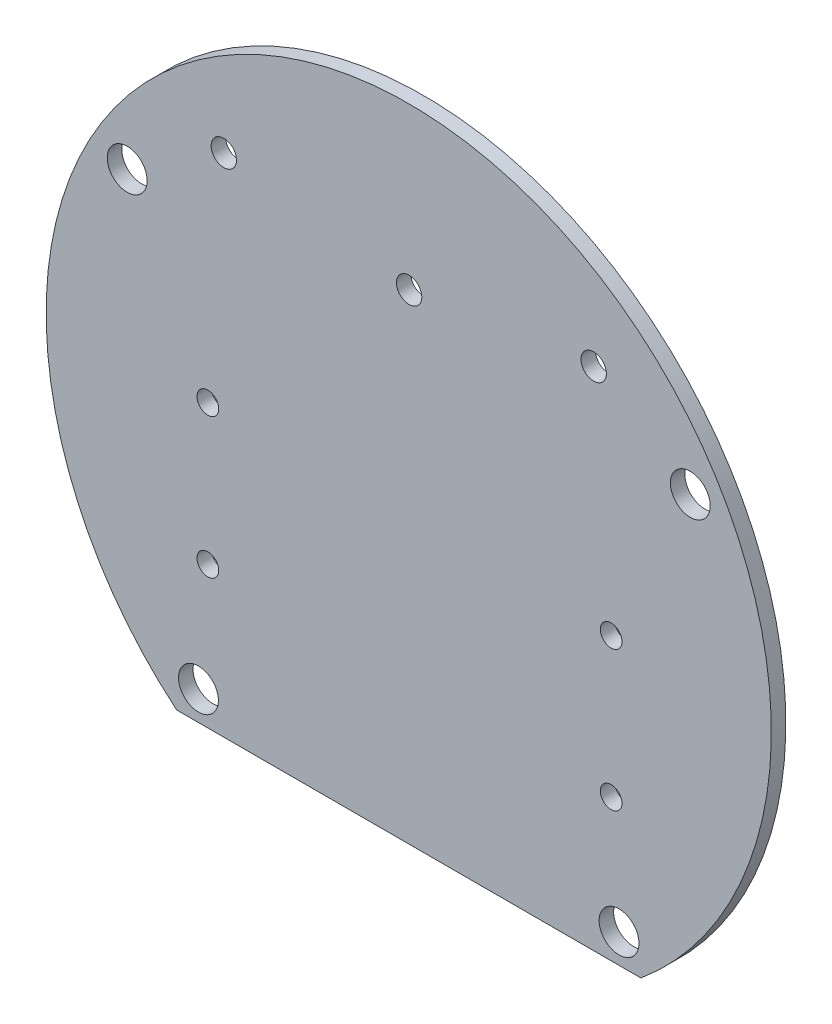
SolidWorks part; units mm, degrees
ref_plane "Plano frontal" through (0, 0, 0) normal (0, 0, 1) x (1, 0, 0)
ref_plane "Plano superior" through (0, 0, 0) normal (0, 1, 0) x (1, 0, 0)
ref_plane "Plano direito" through (0, 0, 0) normal (1, 0, 0) x (0, 0, -1)
sketch "Esboço1" plane through (0, 0, 0) normal (0, 0, 1) x (1, 0, 0)
  circle A0 centre (0, 0) radius 50
  dimension "D1" = 100
extrude "Ressalto-extrusão1" add sketch "Esboço1" along normal blind 2
sketch "Esboço2" plane through (0, 0, 2) normal (0, 0, 1) x (1, 0, 0)
  line L0 (0, 0) -> (0, 68.6386) construction
  line L1 (-61.9657, 0) -> (66.0984, 0) construction
  line L2 (-61.9657, -34.4093) -> (66.0984, -34.4093) construction
  circle A4 centre (-29, -34.4093) radius 2.75
  circle A5 centre (29, -34.4093) radius 2.75
  circle A6 centre (-38.8242, 22.7526) radius 2.75
  circle A7 centre (38.8242, 22.7526) radius 2.75
  point P9 (2.9328, -3.8481)
  dimension "D1" = 58
  dimension "D4" = 45
  dimension "D2" = 45
  dimension "D8" = 5.5
  dimension "D9" = 5.5
  dimension "D10" = 5.5
  dimension "D11" = 5.5
  dimension "D3" = 45
  dimension "D5" = 45
  dimension "D6" = 58
  dimension "D7" = 58
extrude "Corte-extrusão1" cut sketch "Esboço2" against normal blind 2
sketch "Esboço4" plane through (0, 0, 2) normal (0, 0, 1) x (1, 0, 0)
  line L0 (-40.7239, -38.4093) -> (44.5707, -38.4093)
  line L1 (-40.7239, -38.4093) -> (1.9234, -68.0022)
  line L2 (1.9234, -68.0022) -> (44.5707, -38.4093)
  circle A0 centre (-29, -34.4093) radius 2.75 construction
  dimension "D1" = 4
extrude "Corte-extrusão2" cut sketch "Esboço4" against normal blind 10 and the other way through all
sketch "Esboço5" plane through (0, 0, 0) normal (0, 0, -1) x (-1, 0, 0)
  line L0 (65.401, 0) -> (-65.401, 0) construction
  line L2 (0, 53.6175) -> (0, -45.5551) construction
  circle A1 centre (-27.91, -18.86) radius 1.5
  circle A2 centre (27.7, -18.86) radius 1.5
  circle A3 centre (27.7, 0.44) radius 1.5
  circle A4 centre (-27.91, 0.44) radius 1.5
  circle A5 centre (25.5, 31.36) radius 1.75
  circle A6 centre (-0.05, 27.79) radius 1.75
  circle A7 centre (-25.5, 31.36) radius 1.75
  point P4 (0, 0)
  dimension "D1" = 25.5
  dimension "D11" = 27.79
  dimension "D12" = 25.5
  dimension "D2" = 31.36
  dimension "D3" = 0.44
  dimension "D4" = 0.44
  dimension "D5" = 18.86
  dimension "D6" = 27.91
  dimension "D7" = 27.91
  dimension "D8" = 27.7
  dimension "D9" = 27.7
  dimension "D10" = 18.86
  dimension "D13" = 0.05
  dimension "D14" = 31.36
extrude "Corte-extrusão3" cut sketch "Esboço5" against normal blind 10
